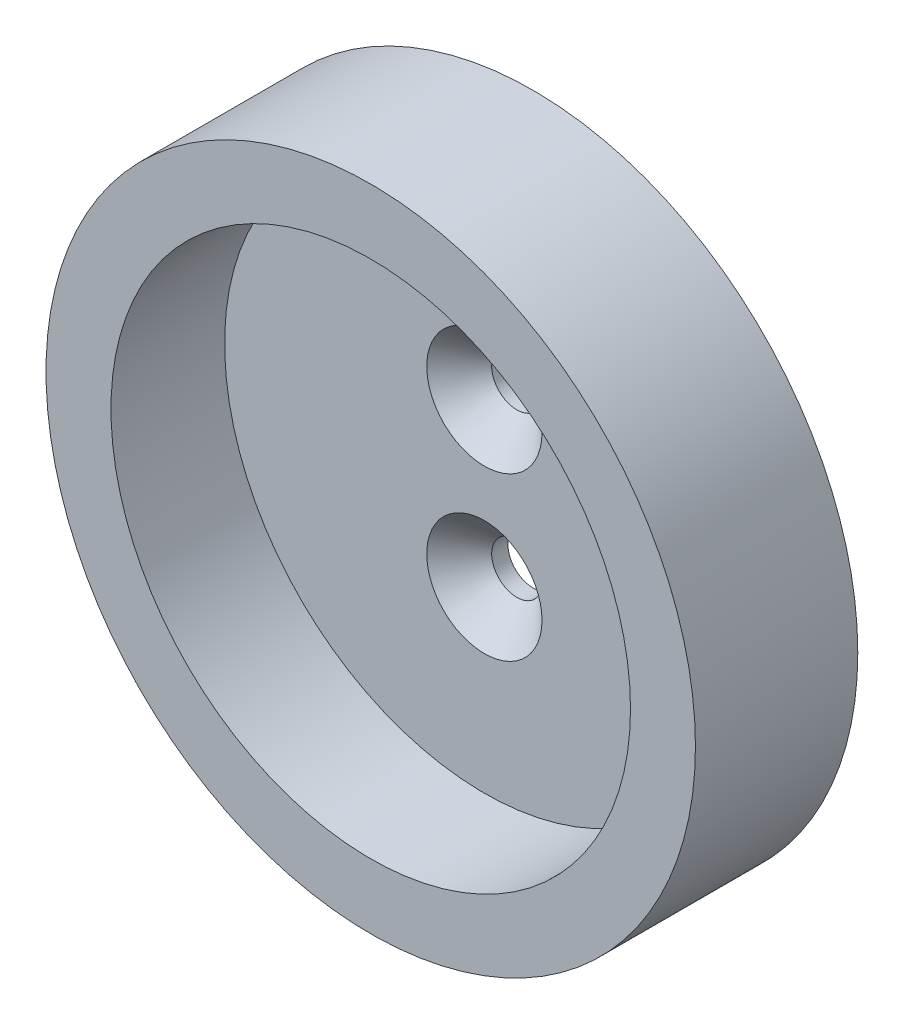
SolidWorks part; units mm, degrees
material "Delrin 2700 NC010, Low Viscosity Acetal Copolymer (SS)"
ref_plane "Front Plane" through (0, 0, 0) normal (0, 0, 1) x (1, 0, 0)
ref_plane "Top Plane" through (0, 0, 0) normal (0, 1, 0) x (1, 0, 0)
ref_plane "Right Plane" through (0, 0, 0) normal (1, 0, 0) x (0, 0, -1)
sketch "Sketch1" plane through (0, 0, 0) normal (0, 0, 1) x (1, 0, 0)
  circle A0 centre (0, 0) radius 20
  dimension "D1" = 40
extrude "Boss-Extrude1" add sketch "Sketch1" along normal blind 10
sketch "Sketch2" plane through (0, 0, 10) normal (0, 0, 1) x (1, 0, 0)
  circle A0 centre (0, 0) radius 16
  dimension "D1" = 32
extrude "Cut-Extrude1" cut sketch "Sketch2" against normal blind 7
sketch "Sketch3" plane through (0, 0, 3) normal (0, 0, 1) x (1, 0, 0)
  line L0 (0, -16) -> (0, 16) construction
  line L1 (-16, 0) -> (16, 0) construction
  circle A0 centre (0, 0) radius 16 construction
  circle A1 centre (0, -5) radius 1.55
  circle A2 centre (0, 5) radius 1.55
  dimension "D1" = 3.1
  dimension "D2" = 5
extrude "Cut-Extrude2" cut sketch "Sketch3" against normal through all
chamfer "Chamfer1" distance 2 angle 45 2 edges at (1.55, -5, 3) (-1.55, 5, 3)
